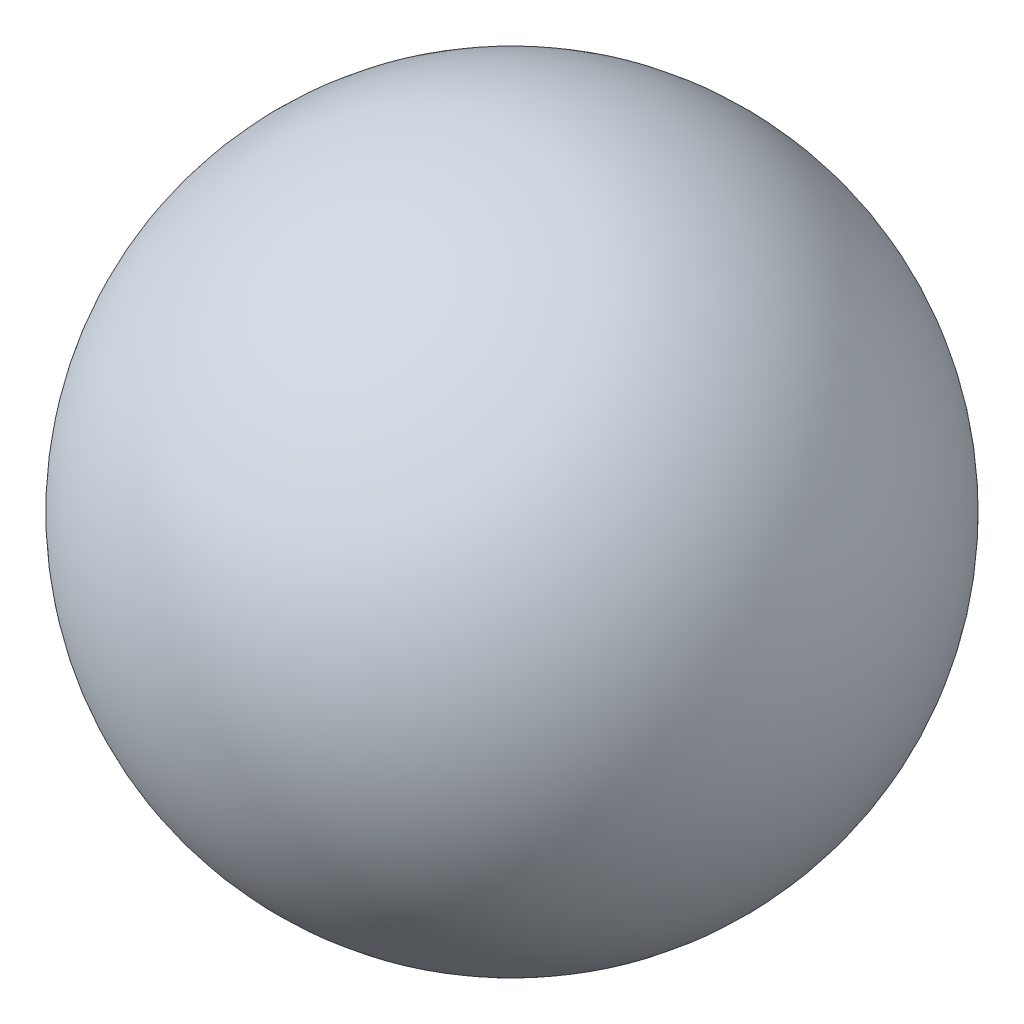
SolidWorks part; units mm, degrees
ref_plane "Front Plane" through (0, 0, 0) normal (0, 0, 1) x (1, 0, 0)
ref_plane "Top Plane" through (0, 0, 0) normal (0, 1, 0) x (1, 0, 0)
ref_plane "Right Plane" through (0, 0, 0) normal (1, 0, 0) x (0, 0, -1)
sketch "Sketch3" plane through (0, 0, 0) normal (0, 0, 1) x (1, 0, 0)
  line L0 (0, 0) -> (0, 49.8875) construction
  line L1 (0, 20) -> (0, -20)
  arc A0 (0, -20) -> (0, 20) centre (0, 0) ccw
  dimension "D1" = 40
revolve "Revolve1" add sketch "Sketch3" angle 360 about L0
